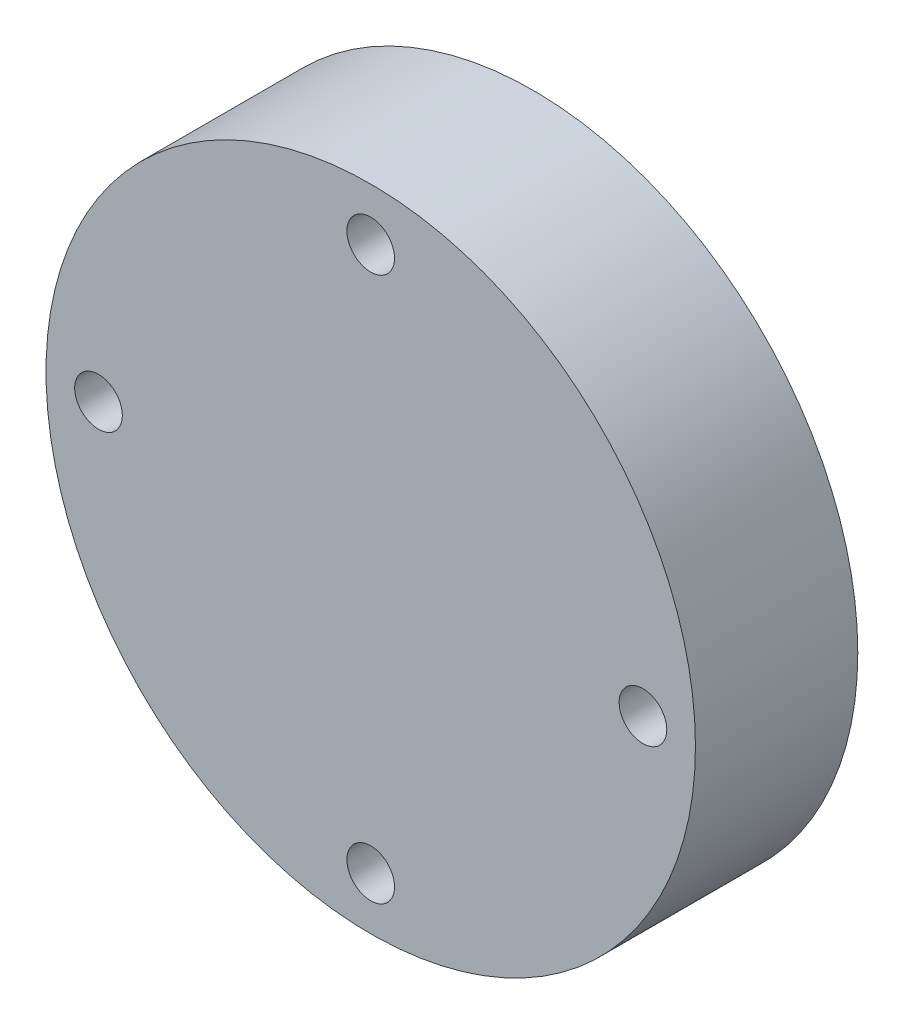
SolidWorks part; units mm, degrees
ref_plane "Front Plane" through (0, 0, 0) normal (0, 0, 1) x (1, 0, 0)
ref_plane "Top Plane" through (0, 0, 0) normal (0, 1, 0) x (1, 0, 0)
ref_plane "Right Plane" through (0, 0, 0) normal (1, 0, 0) x (0, 0, -1)
sketch "Sketch1" plane through (0, 0, 0) normal (0, 0, 1) x (1, 0, 0)
  circle A0 centre (0, 0) radius 30
  dimension "D1" = 60
extrude "Boss-Extrude1" add sketch "Sketch1" along normal blind 15
sketch "Sketch2" plane through (0, 0, 0) normal (0, 0, 1) x (1, 0, 0)
  line L0 (-30, 0) -> (30, 0) construction
  circle A0 centre (0, 25.15) radius 2.2
  circle A1 centre (0, 0) radius 30 construction
  circle A2 centre (25.15, 0) radius 2.2
  circle A3 centre (0, -25.15) radius 2.2
  circle A4 centre (-25.15, 0) radius 2.2
  point P17 (0, 0)
  dimension "D1" = 4.4
  dimension "D2" = 25.15
  dimension "D3" = 4
extrude "Cut-Extrude1" cut sketch "Sketch2" along normal up to surface (15 mm away) up to face at (30, 0, 15)
sketch "Sketch3" plane through (0, 0, 0) normal (0, 0, 1) x (1, 0, 0)
  circle A0 centre (0, 25.15) radius 4
  circle A1 centre (25.15, 0) radius 4
  circle A2 centre (0, -25.15) radius 4
  circle A3 centre (-25.15, 0) radius 4
  point P11 (0, 0)
  dimension "D1" = 8
  dimension "D2" = 4
extrude "Cut-Extrude2" cut sketch "Sketch3" along normal blind 4.5
sketch "Sketch5" plane through (0, 0, 0) normal (0, 0, 1) x (1, 0, 0)
  circle A0 centre (0, 0) radius 8
  dimension "D1" = 16
extrude "Boss-Extrude2" add sketch "Sketch5" against normal blind 1.5
ref_plane "Plane2" through (0, 0, -1.5) normal (0, 0, 1) x (1, 0, 0)
sketch "Sketch8" plane through (0, 0, -1.5) normal (0, 0, 1) x (1, 0, 0)
  line L0 (0, 8) -> (0, -8) construction
  line L2 (-8, 0) -> (8, 0) construction
  circle A0 centre (0, 0) radius 8 construction
  circle A1 centre (0, 0) radius 8 construction
  circle A2 centre (0, 0) radius 3.25
  dimension "D1" = 6.5
extrude "Cut-Extrude3" cut sketch "Sketch8" along normal blind 7
